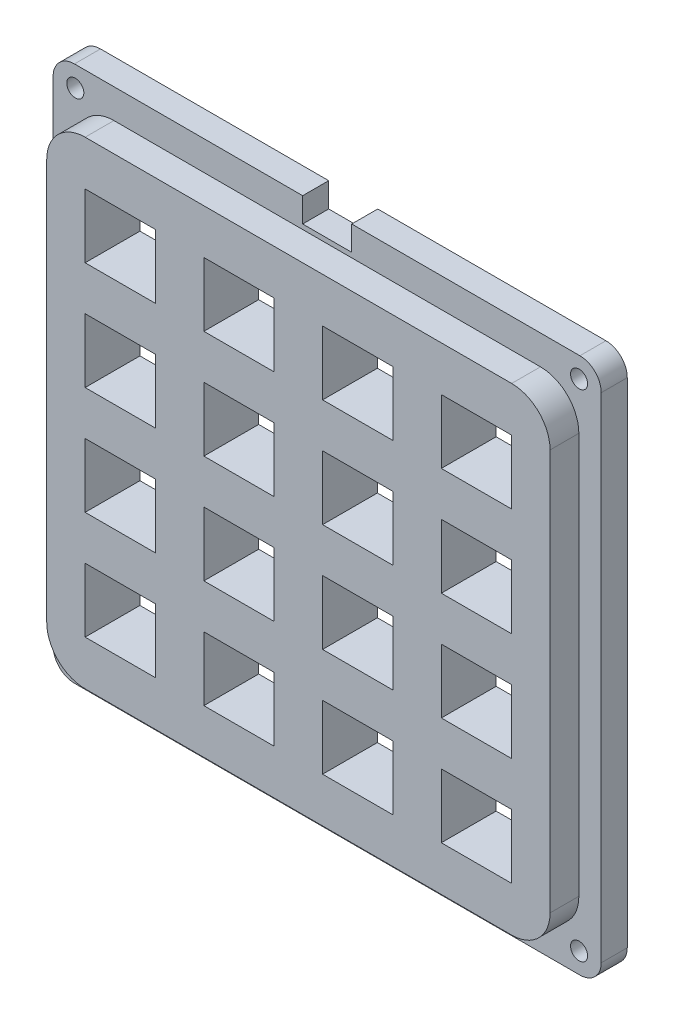
SolidWorks part; units mm, degrees
ref_plane "Front" through (0, 0, 0) normal (0, 0, 1) x (1, 0, 0)
ref_plane "Top" through (0, 0, 0) normal (0, 1, 0) x (1, 0, 0)
ref_plane "Right" through (0, 0, 0) normal (1, 0, 0) x (0, 0, -1)
sketch "Sketch1" plane through (0, 0, 0) normal (0, 0, 1) x (1, 0, 0)
  line L0 (-32.639, 0) -> (32.639, 0) construction
  line L1 (-30.099, 31.9405) -> (30.099, 31.9405)
  line L2 (-32.639, 29.4005) -> (-32.639, -29.4005)
  line L3 (-30.099, -31.9405) -> (30.099, -31.9405)
  line L4 (32.639, 29.4005) -> (32.639, -29.4005)
  line L5 (0, 29.0195) -> (0, 0) construction
  line L6 (-2.921, 31.9405) -> (2.921, 31.9405)
  line L7 (-2.921, 31.9405) -> (-2.921, 29.0195)
  line L8 (-2.921, 29.0195) -> (2.921, 29.0195)
  line L9 (2.921, 31.9405) -> (2.921, 29.0195)
  arc A0 (-30.099, 31.9405) -> (-32.639, 29.4005) centre (-30.099, 29.4005) ccw
  arc A1 (32.639, 29.4005) -> (30.099, 31.9405) centre (30.099, 29.4005) ccw
  arc A2 (-30.099, -31.9405) -> (-32.639, -29.4005) centre (-30.099, -29.4005) cw
  arc A3 (32.639, -29.4005) -> (30.099, -31.9405) centre (30.099, -29.4005) cw
  point P6 (0, 0)
  point P10 (-32.639, 31.9405)
  point P13 (32.639, 31.9405)
  point P16 (-32.639, -31.9405)
  dimension "D3" = 2.54
  dimension "D1" = 63.881
  dimension "D2" = 65.278
  dimension "D4" = 2.921
  dimension "D5" = 5.842
extrude "base" add sketch "Sketch1" along normal blind 3.0988 contours A3 L4 A1 L1 L9 L8 L7 A0 L2 A2 L3
sketch "Sketch4" plane through (0, 0, 3.0988) normal (0, 0, 1) x (1, 0, 0)
  line L0 (-30, 0) -> (30, 0) construction
  line L1 (-30, 29.5) -> (30, 29.5) construction
  line L2 (-30, 29.5) -> (-30, -29.5) construction
  line L3 (-30, -29.5) -> (30, -29.5) construction
  line L4 (30, 29.5) -> (30, -29.5) construction
  circle A0 centre (-30, 29.5) radius 1.016
  circle A1 centre (30, 29.5) radius 1.016
  circle A2 centre (30, -29.5) radius 1.016
  circle A3 centre (-30, -29.5) radius 1.016
  point P7 (0, 0)
  dimension "D1" = 2.032
  dimension "D2" = 59
  dimension "D3" = 60
extrude "mount holes" cut sketch "Sketch4" against normal through all
sketch "Sketch2" plane through (0, 0, 3.0988) normal (0, 0, 1) x (1, 0, 0)
  line L0 (0, 28.448) -> (0, -28.448) construction
  line L1 (-25.4, 28.448) -> (25.4, 28.448)
  line L2 (-29.972, 23.876) -> (-29.972, -23.876)
  line L3 (-25.4, -28.448) -> (25.4, -28.448)
  line L4 (29.972, 23.876) -> (29.972, -23.876)
  arc A0 (-25.4, 28.448) -> (-29.972, 23.876) centre (-25.4, 23.876) ccw
  arc A1 (-25.4, -28.448) -> (-29.972, -23.876) centre (-25.4, -23.876) cw
  arc A2 (29.972, -23.876) -> (25.4, -28.448) centre (25.4, -23.876) cw
  arc A3 (29.972, 23.876) -> (25.4, 28.448) centre (25.4, 23.876) ccw
  point P6 (0, 0)
  point P10 (-29.972, 28.448)
  point P13 (-29.972, -28.448)
  point P18 (29.972, 28.448)
  dimension "D3" = 4.572
  dimension "D1" = 59.944
  dimension "D2" = 56.896
extrude "Extrude2" add sketch "Sketch2" along normal blind 3.429
sketch "Sketch3" plane through (0, 0, 6.5278) normal (0, 0, 1) x (1, 0, 0)
  line L1 (-25.4, 23.114) -> (-17.018, 23.114)
  line L2 (-25.4, 23.114) -> (-25.4, 15.494)
  line L3 (-25.4, 15.494) -> (-17.018, 15.494)
  line L4 (-17.018, 23.114) -> (-17.018, 15.494)
  dimension "D1" = 8.382
  dimension "D2" = 7.62
  dimension "D3" = 25.4
  dimension "D4" = 23.114
extrude "key" cut sketch "Sketch3" against normal through all
pattern_linear "keys" count 4 spacing 14.1402 along (1, 0, 0) count 4 spacing 12.8694 along (0, -1, 0) of "key"
